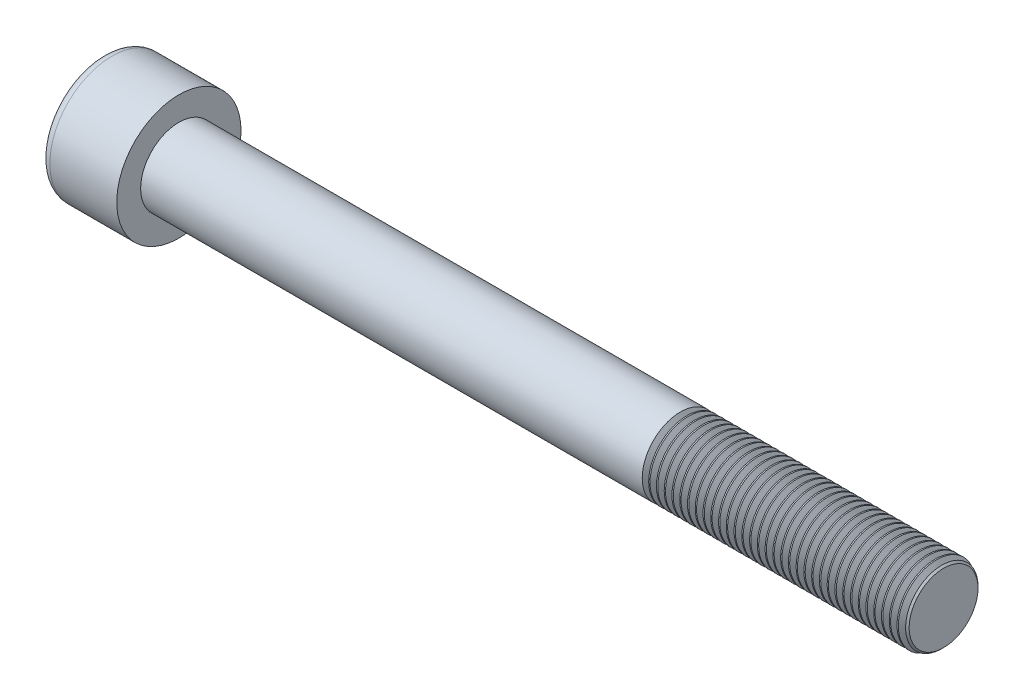
SolidWorks part; units mm, degrees
ref_plane "Front" through (0, 0, 0) normal (0, 0, 1) x (1, 0, 0)
ref_plane "Top" through (0, 0, 0) normal (0, 1, 0) x (1, 0, 0)
ref_plane "Right" through (0, 0, 0) normal (1, 0, 0) x (0, 0, -1)
sketch "Sketch1" plane through (0, 0, 0) normal (1, 0, 0) x (0, 0, -1)
  circle A0 centre (0, 0) radius 6.5
  dimension "dk" = 13
extrude "BaseHead" add sketch "Sketch1" along normal blind 8
sketch "Sketch2" plane through (8, 0, 0) normal (1, 0, 0) x (0, 0, -1)
  circle A0 centre (0, 0) radius 4
  dimension "d" = 8
extrude "BaseBody" add sketch "Sketch2" along normal blind 80
cosmetic thread "ThreadCosmetic1" [suppressed] parameters "b"=28, "D2"=6.647
sketch "Sketch3" plane through (0, 0, 0) normal (1, 0, 0) x (0, 0, -1)
  line L1 (3.4641, 0) -> (1.7321, 3)
  line L2 (1.7321, 3) -> (-1.7321, 3)
  line L3 (-1.7321, 3) -> (-3.4641, 0)
  line L4 (-3.4641, 0) -> (-1.7321, -3)
  line L5 (-1.7321, -3) -> (1.7321, -3)
  line L6 (1.7321, -3) -> (3.4641, 0)
  circle A0 centre (0, 0) radius 3 construction
  dimension "s" = 6
  dimension "e" = 6.9282
extrude "HexagonSocket" cut sketch "Sketch3" along normal blind 4
sketch "Sketch4" plane through (-4.1961, 0.75, 0) normal (0, 0, 1) x (-1, 0, 0)
  line L0 (-8.1961, 3.75) -> (-9.9282, 0.75)
  line L2 (-9.9282, 0.75) -> (-8.1961, 0.75)
  line L3 (-8.1961, 0.75) -> (-8.1961, 3.75)
  line L4 (-5.0351, 0.75) -> (0.839, 0.75) construction
  line L5 (-92.1961, 0.75) -> (-12.1961, 0.75) construction
  line L6 (-12.1961, 0.75) -> (-4.1961, 0.75) construction
  dimension "m" = 60
revolve "Cut-Revolve1" cut sketch "Sketch4" angle 360 about L4
fillet "HeadFillet" [suppressed] radius 0.4
fillet "TopFillet" radius 1 1 edges at (0, 0, -6.5)
chamfer "Chamfer1" distance 0.4 angle 45 1 edges at (88, 0, -4)
sketch "Sketch5" plane through (0, 0, 0) normal (0, 0, 1) x (1, 0, 0)
  line L0 (87.6, 3.4141) -> (87.9383, 4)
  line L1 (87.9383, 4) -> (87.9383, 4.6765)
  line L2 (87.9383, 4.6765) -> (87.2618, 4.6765)
  line L3 (87.2618, 4.6765) -> (87.2618, 4)
  line L4 (87.2618, 4) -> (87.6, 3.4141)
  line L5 (0, 0) -> (7.8886, 0) construction
  line L6 (87.6, -4) -> (87.6, 4) construction
  dimension "D1" = 8
  dimension "D2" = 0.6765
revolve "Cut-Revolve10" cut sketch "Sketch5" angle 360 about L5
pattern_linear "LPattern10" count 34 spacing 0.8118 along (-1, 0, 0) of "Cut-Revolve10"
equation "\"r1@TopFillet\" = \"d@Sketch2\" / 8"
equation "\"D1@Chamfer1\" = \"r@HeadFillet\""
equation "\"D1@Sketch5\" = \"d@Sketch2\""
equation "\"D2@Sketch5\" =  ( \"d@Sketch2\" - \"D2@ThreadCosmetic1\" )  / 2"
equation "\"D3@LPattern10\" = \"D2@Sketch5\" * 1.2"
equation "\"D1@LPattern10\" = \"b@ThreadCosmetic1\" / \"D3@LPattern10\""
